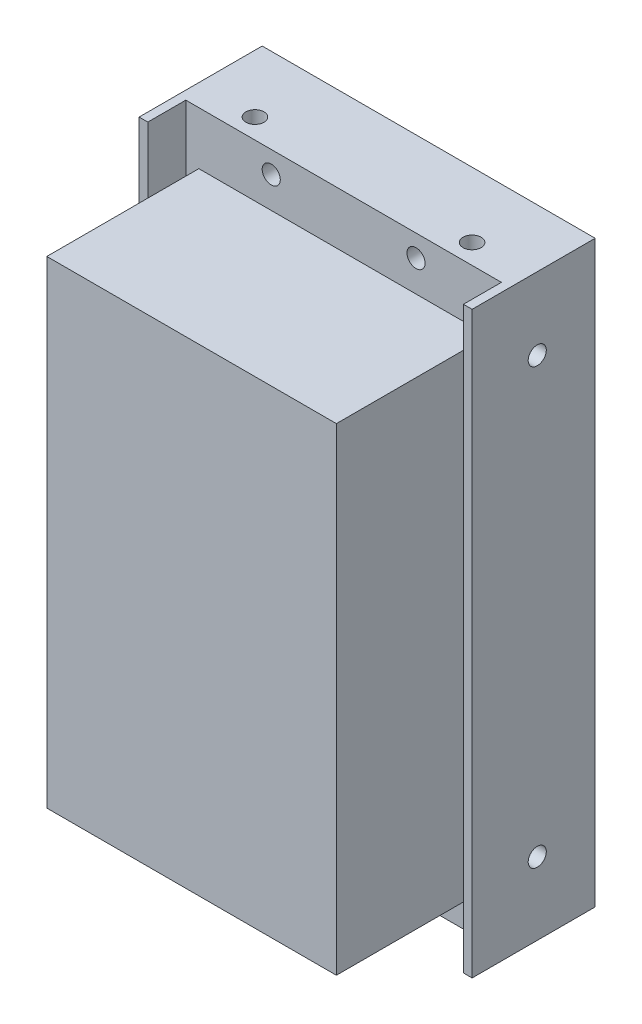
SolidWorks part; units mm, degrees
ref_plane "Front Plane" through (0, 0, 0) normal (0, 0, 1) x (1, 0, 0)
ref_plane "Top Plane" through (0, 0, 0) normal (0, 1, 0) x (1, 0, 0)
ref_plane "Right Plane" through (0, 0, 0) normal (1, 0, 0) x (0, 0, -1)
sketch "Sketch1" plane through (0, 0, 0) normal (0, 1, 0) x (1, 0, 0)
  line L1 (-23, 11.75) -> (23, 11.75)
  line L2 (-23, 11.75) -> (-23, 0)
  line L3 (-23, 0) -> (23, 0)
  line L4 (23, 11.75) -> (23, 0)
  line L5 (-23, 11.75) -> (23, 0) construction
  line L6 (-23, 0) -> (23, 11.75) construction
  point P0 (0, 5.875)
  point P6 (0, 0)
  dimension "D1" = 46
  dimension "D2" = 11.75
extrude "Boss-Extrude1" add sketch "Sketch1" along normal blind 80
sketch "Sketch2" plane through (0, 0, 0) normal (0, 1, 0) x (1, 0, 0)
  line L0 (23, 11.75) -> (-23, 11.75) construction
  line L1 (-23, 0) -> (-21.8, 0)
  line L2 (-23, 0) -> (-23, -5.25)
  line L3 (-23, -5.25) -> (-21.8, -5.25)
  line L4 (-21.8, 0) -> (-21.8, -5.25)
  line L5 (23, 0) -> (21.8, 0)
  line L6 (23, 0) -> (23, -5.25)
  line L7 (23, -5.25) -> (21.8, -5.25)
  line L8 (21.8, 0) -> (21.8, -5.25)
  dimension "D1" = 1.2
  dimension "D2" = 17
extrude "Boss-Extrude2" add sketch "Sketch2" along normal blind 80
sketch "Sketch3" plane through (0, 0, 0) normal (0, 0, 1) x (1, 0, 0)
  line L0 (-21.8, 0) -> (21.8, 0) construction
  line L1 (-20, 72.7) -> (20, 72.7)
  line L2 (-20, 72.7) -> (-20, 6.7)
  line L3 (-20, 6.7) -> (20, 6.7)
  line L4 (20, 72.7) -> (20, 6.7)
  line L5 (0, 6.7) -> (0, 72.7) construction
  line L6 (-20, 39.7) -> (20, 39.7) construction
  point P260 (0, 39.7)
  dimension "D1" = 66
  dimension "D2" = 40
  dimension "D3" = 6.7
extrude "Circuit Board clearance" add sketch "Sketch3" along normal blind 21
hole_wizard "M3x0.5 Tapped Hole1" positions "Sketch4" profile "Sketch5" tap size "M3x0.5" standard "ANSI Metric" end condition through all
sketch "Sketch4" plane through (0, 0, 0) normal (0, 0, 1) x (1, 0, 0)
  line L0 (-21.8, 40) -> (21.8, 40) construction
  line L1 (-21.8, 80) -> (-21.8, 0) construction
  line L2 (21.8, 80) -> (21.8, 0) construction
  line L6 (0, 80) -> (0, 0) construction
  line L7 (-21.8, 80) -> (21.8, 80) construction
  point P0 (-10, 77)
  point P2 (10, 77)
  point P4 (-10, 3)
  point P6 (10, 3)
  point P27 (0, 0)
  point P28 (0, 0)
  point P29 (0, 0)
  dimension "D1" = 20
  dimension "D2" = 3
cosmetic thread "Hole Thread1" parameters "D2"=3
cosmetic thread "Hole Thread2" parameters "D2"=3
cosmetic thread "Hole Thread3" parameters "D2"=3
cosmetic thread "Hole Thread4" parameters "D2"=3
sketch "Sketch5" plane through (-10, 77, 0) normal (1, 0, 0) x (0, -1, 0)
  line L0 (0, 0) -> (0, 11.75)
  line L1 (0, 11.75) -> (1.25, 11.75)
  line L2 (1.25, 11.75) -> (1.25, 0)
  line L5 (1.25, 0) -> (0, 0)
  line L11 (0, -6.35) -> (0, 107.95) construction
  dimension "Thru Tap Drill Dia." = 2.5
  dimension "Thru Tap Drill Depth" = 11.75
hole_wizard "M3x0.5 Tapped Hole2" positions "Sketch6" profile "Sketch7" tap size "M3x0.5" standard "ANSI Metric"
sketch "Sketch6" plane through (0, 80, 0) normal (0, 1, 0) x (1, 0, 0)
  line L0 (0, 0) -> (0, 11.75) construction
  line L1 (23, 11.75) -> (-23, 11.75) construction
  line L3 (-21.8, 0) -> (21.8, 0) construction
  point P0 (-15, 2.75)
  point P2 (15, 2.75)
  point P13 (0, 0)
  dimension "D1" = 30
  dimension "D2" = 2.75
sketch "Sketch7" plane through (-15, 80, -2.75) normal (1, 0, 0) x (0, 0, 1)
  line L0 (0, 0) -> (0, 5.7511)
  line L1 (0, 5.7511) -> (1.25, 5)
  line L2 (1.25, 5) -> (1.25, 0)
  line L5 (1.25, 0) -> (0, 0)
  line L10 (0, 5.7511) -> (-1.25, 5) construction
  line L11 (0, -6.35) -> (0, 107.95) construction
  dimension "Tap Drill Dia." = 2.5
  dimension "Tap Drill Depth" = 5
  dimension "Drill Angle" = 118
cosmetic thread "Hole Thread5" parameters "D1"=5, "D2"=3
cosmetic thread "Hole Thread6" parameters "D1"=5, "D2"=3
hole_wizard "M3x0.5 Tapped Hole3" positions "Sketch8" profile "Sketch10" tap size "M3x0.5" standard "ANSI Metric" end condition through all
sketch "Sketch8" plane through (23, 0, 0) normal (1, 0, 0) x (0, 0, -1)
  line L0 (11.75, 80) -> (11.75, 0) construction
  line L1 (-5.25, 0) -> (11.75, 0) construction
  point P0 (3.75, 70)
  point P2 (3.75, 10)
  point P7 (0, 0)
  dimension "D1" = 8
  dimension "D2" = 60
  dimension "D3" = 10
sketch "Sketch10" plane through (23, 70, -3.75) normal (0, 1, 0) x (0, 0, -1)
  line L0 (0, 0) -> (0, 46)
  line L1 (0, 46) -> (1.25, 46)
  line L2 (1.25, 46) -> (1.25, 0)
  line L5 (1.25, 0) -> (0, 0)
  line L11 (0, -6.35) -> (0, 107.95) construction
  dimension "Thru Tap Drill Dia." = 2.5
  dimension "Thru Tap Drill Depth" = 46
cosmetic thread "Hole Thread7" parameters "D2"=3
cosmetic thread "Hole Thread8" parameters "D2"=3
